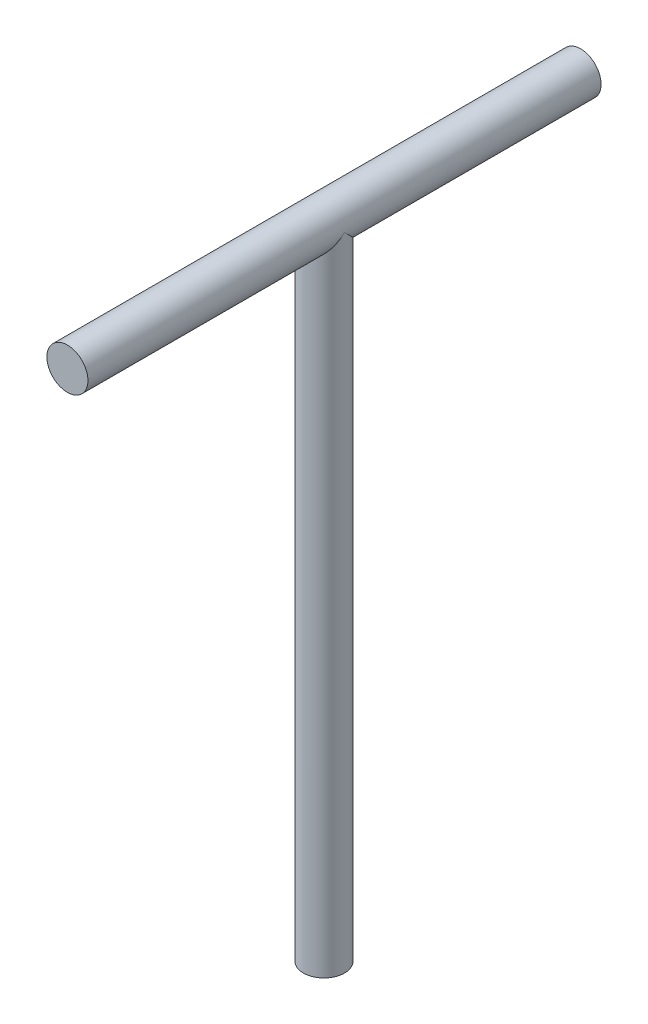
SolidWorks part; units mm, degrees
material "Alloy Steel"
ref_plane "Front Plane" through (0, 0, 0) normal (0, 0, 1) x (1, 0, 0)
ref_plane "Top Plane" through (0, 0, 0) normal (0, 1, 0) x (1, 0, 0)
ref_plane "Right Plane" through (0, 0, 0) normal (1, 0, 0) x (0, 0, -1)
sketch "Sketch1" plane through (0, 0, 0) normal (0, 0, 1) x (1, 0, 0)
  circle A0 centre (0, 0) radius 16
  dimension "D1" = 32
extrude "Boss-Extrude1" add sketch "Sketch1" along normal mid plane 400
sketch "Sketch3" plane through (0, 0, 0) normal (0, 1, 0) x (1, 0, 0)
  circle A0 centre (0, 0) radius 16
  dimension "D1" = 32
extrude "Boss-Extrude2" add sketch "Sketch3" against normal blind 500
